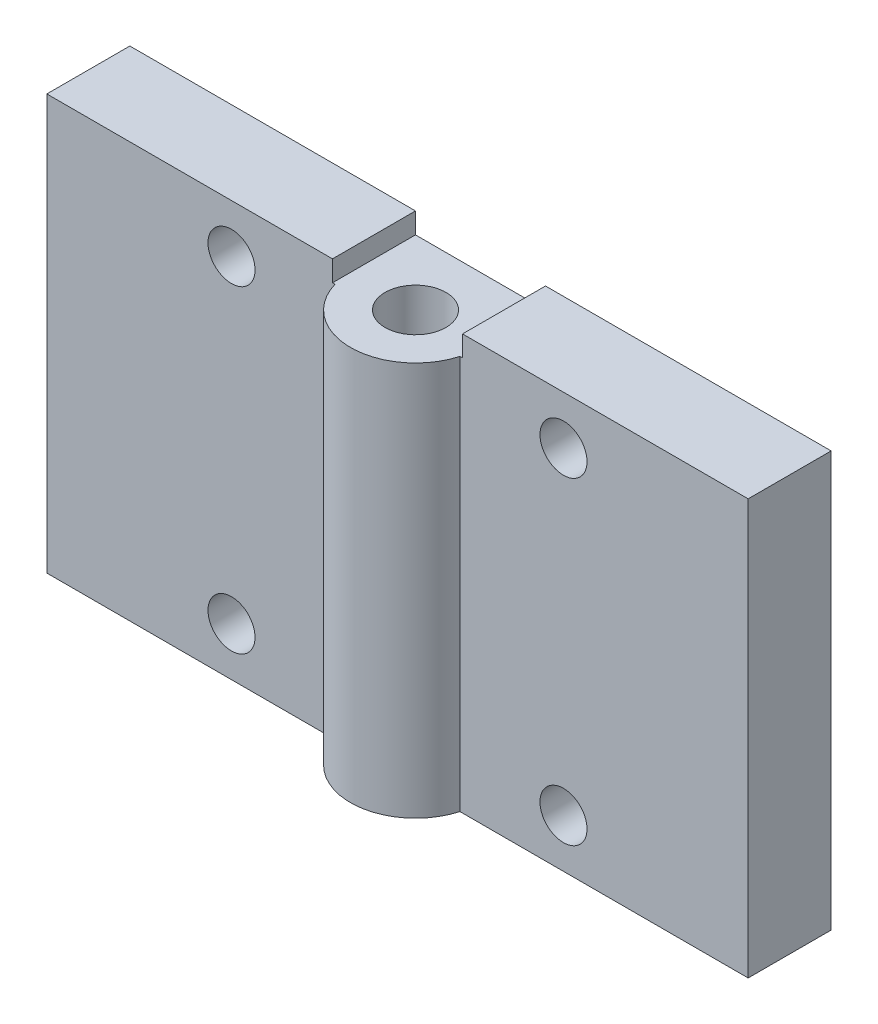
SolidWorks part; units mm, degrees
ref_plane "前视基准面" through (0, 0, 0) normal (0, 0, 1) x (1, 0, 0)
ref_plane "上视基准面" through (0, 0, 0) normal (0, 1, 0) x (1, 0, 0)
ref_plane "右视基准面" through (0, 0, 0) normal (1, 0, 0) x (0, 0, -1)
ref_plane "基准面4" through (0, 253.5, 0) normal (0, 1, 0) x (1, 0, 0)
sketch "草图1" plane through (0, 253.5, 0) normal (0, 1, 0) x (1, 0, 0)
  line L0 (264.5166, -508.1) -> (285.35, -508.1)
  line L1 (285.35, -508.1) -> (285.35, -502.1)
  line L2 (285.35, -502.1) -> (234.65, -502.1)
  line L3 (234.65, -502.1) -> (234.65, -508.1)
  line L4 (234.65, -508.1) -> (255.4834, -508.1)
  arc A0 (255.4834, -508.1) -> (264.5166, -508.1) centre (260, -506.8) ccw
extrude "凸台-拉伸1" add sketch "草图1" against normal blind 28.5
sketch "草图2" plane through (0, 253.5, 0) normal (0, 1, 0) x (-1, 0, 0)
  line L0 (-264.7, 502.1) -> (-285.35, 502.1)
  line L1 (-285.35, 502.1) -> (-285.35, 508.1)
  line L2 (-285.35, 508.1) -> (-264.7, 508.1)
  line L3 (-264.7, 508.1) -> (-264.7, 502.1)
extrude "凸台-拉伸2" add sketch "草图2" along normal blind 1.5
sketch "草图3" plane through (0, 253.5, 0) normal (0, 1, 0) x (-1, 0, 0)
  line L0 (-255.3, 508.1) -> (-234.65, 508.1)
  line L1 (-234.65, 508.1) -> (-234.65, 502.1)
  line L2 (-234.65, 502.1) -> (-255.3, 502.1)
  line L3 (-255.3, 502.1) -> (-255.3, 508.1)
extrude "凸台-拉伸3" add sketch "草图3" along normal blind 1.5
hole_wizard "Ø4.4 (4.4) 直径孔1" positions "草图5" profile "草图4" hole size "Ø4.4" standard "ANSI Metric"
sketch "草图5" plane through (0, 253.5, 0) normal (0, 1, 0) x (1, 0, 0)
  point P0 (260, -506.8)
sketch "草图4" plane through (260, 253.5, 506.8) normal (1, 0, 0) x (0, 0, 1)
  line L0 (0, 0) -> (0, 28.5)
  line L1 (0, 28.5) -> (2.2, 28.5)
  line L2 (2.2, 28.5) -> (2.2, 0)
  line L5 (2.2, 0) -> (0, 0)
  line L11 (0, -6.35) -> (0, 107.95) construction
  dimension "通孔孔直径" = 4.4
  dimension "通孔孔深度" = 28.5
hole_wizard "Ø3.4 (3.4) 直径孔1" positions "草图7" profile "草图6" hole size "Ø3.4" standard "ANSI Metric"
sketch "草图7" plane through (0, 0, 502.1) normal (0, 0, -1) x (-1, 0, 0)
  point P0 (-248, 228.5)
  point P1 (-248, 251.5)
  point P2 (-272, 251.5)
  point P3 (-272, 228.5)
sketch "草图6" plane through (248, 228.5, 502.1) normal (1, 0, 0) x (0, 1, 0)
  line L0 (0, 0) -> (0, 9.4)
  line L1 (0, 9.4) -> (1.7, 9.4)
  line L2 (1.7, 9.4) -> (1.7, 0)
  line L5 (1.7, 0) -> (0, 0)
  line L11 (0, -6.35) -> (0, 107.95) construction
  dimension "通孔孔直径" = 3.4
  dimension "通孔孔深度" = 9.4
